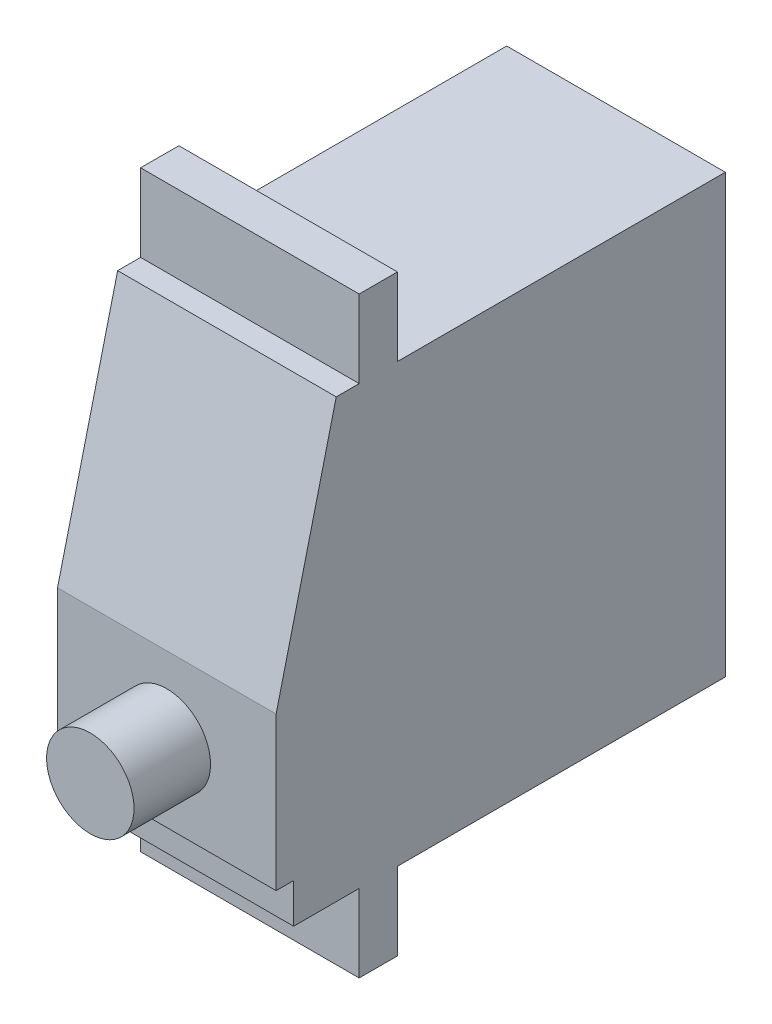
SolidWorks part; units mm, degrees
ref_plane "Front Plane" through (0, 0, 0) normal (0, 0, 1) x (1, 0, 0)
ref_plane "Top Plane" through (0, 0, 0) normal (0, 1, 0) x (1, 0, 0)
ref_plane "Right Plane" through (0, 0, 0) normal (1, 0, 0) x (0, 0, -1)
ref_plane "Plane1" through (10, 0, 0) normal (1, 0, 0) x (0, 0, -1)
sketch "Sketch1" plane through (10, 0, 0) normal (1, 0, 0) x (0, 0, -1)
  line L0 (0, 29.3791) -> (-35.6, 29.3791)
  line L1 (-35.6, 29.3791) -> (-41.1, 7)
  line L2 (-41.1, 7) -> (-41.1, -17.7209)
  line L3 (-41.1, -17.7209) -> (0, -17.7209)
  line L4 (0, -17.7209) -> (0, 29.3791)
extrude "Boss-Extrude1" add sketch "Sketch1" against normal blind 20
sketch "Sketch2" plane through (10, 0, 0) normal (1, 0, 0) x (0, 0, -1)
  line L0 (-30, -10.6209) -> (-30, -17.7209)
  line L1 (-30, -17.7209) -> (0, -17.7209)
  line L2 (0, -17.7209) -> (0, -10.6209)
  line L3 (0, -10.6209) -> (-30, -10.6209)
extrude "Cut-Extrude1" cut sketch "Sketch2" against normal through all
sketch "Sketch3" plane through (10, 0, 0) normal (1, 0, 0) x (0, 0, -1)
  line L0 (-33.5, -10.6209) -> (-41.1, -10.6209)
  line L1 (-41.1, -10.6209) -> (-41.1, -17.7209)
  line L2 (-41.1, -17.7209) -> (-33.5, -17.7209)
  line L3 (-33.5, -17.7209) -> (-33.5, -10.6209)
extrude "Cut-Extrude2" cut sketch "Sketch3" against normal through all
sketch "Sketch4" plane through (10, 0, 0) normal (1, 0, 0) x (0, 0, -1)
  line L0 (-39.5, -7) -> (-41.1, -7)
  line L1 (-41.1, -7) -> (-41.1, -10.6209)
  line L2 (-41.1, -10.6209) -> (-39.5, -10.6209)
  line L3 (-39.5, -10.6209) -> (-39.5, -7)
extrude "Cut-Extrude3" cut sketch "Sketch4" against normal through all
ref_plane "Plane2" through (-9.8732, 0, -0.0388) normal (-1, 0, -0.0039) x (0, -1, 0)
sketch "Sketch6" plane through (10, 0, 0) normal (1, 0, 0) x (0, 0, -1)
  line L0 (-33.5, 29.3791) -> (-30, 29.3791)
  line L1 (-30, 29.3791) -> (-30, 36.4791)
  line L2 (-30, 36.4791) -> (-33.5, 36.4791)
  line L3 (-33.5, 36.4791) -> (-33.5, 29.3791)
extrude "Boss-Extrude2" add sketch "Sketch6" against normal up to surface up to plane "Plane2"
sketch "Sketch7" plane through (0, 0, 41.1) normal (0, 0, 1) x (1, 0, 0)
  circle A0 centre (0, 0) radius 4
  dimension "D1" = 8
extrude "Boss-Extrude3" add sketch "Sketch7" along normal blind 7 contours A0
other "Move Face2" face at (4, 0, 48.1) parameters "D1"=6
other "Move Face3" face at (4, 0, 54.1) parameters "D1"=6
